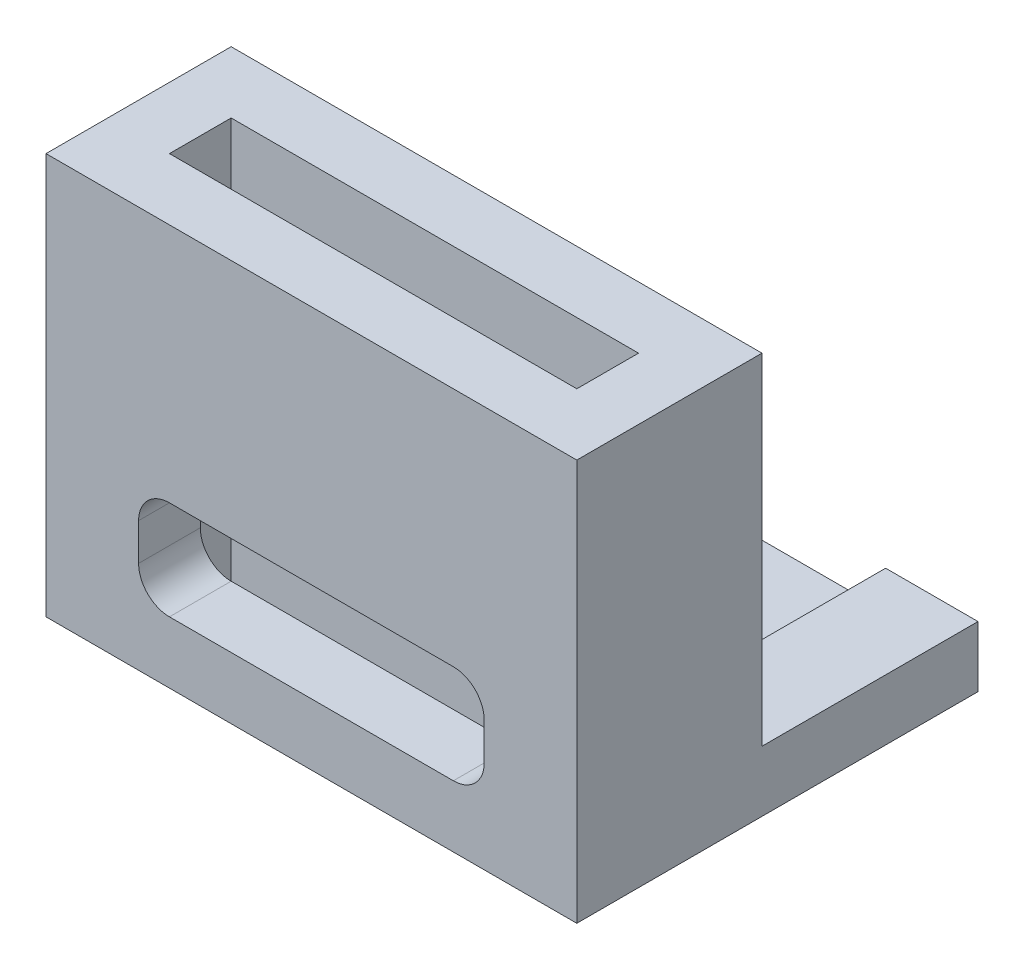
SolidWorks part; units mm, degrees
ref_plane "Front Plane" through (0, 0, 0) normal (0, 0, 1) x (1, 0, 0)
ref_plane "Top Plane" through (0, 0, 0) normal (0, 1, 0) x (1, 0, 0)
ref_plane "Right Plane" through (0, 0, 0) normal (1, 0, 0) x (0, 0, -1)
sketch "Sketch1" plane through (0, 0, 0) normal (0, 1, 0) x (1, 0, 0)
  line L0 (0, 0) -> (13.2, 0)
  line L1 (0, 0) -> (0, 2)
  line L2 (0, 2) -> (13.2, 2)
  line L3 (13.2, 2) -> (13.2, 0)
  line L4 (15.2, 4) -> (15.2, -2)
  line L5 (-2, -2) -> (15.2, -2)
  line L6 (-2, -2) -> (-2, 4)
  line L7 (-2, 4) -> (15.2, 4)
  dimension "D1" = 2
extrude "Boss-Extrude1" add sketch "Sketch1" along normal blind 13
sketch "Sketch2" plane through (0, 0, 2) normal (0, 0, 1) x (1, 0, 0)
  line L4 (2, 5.2) -> (11.2, 5.2)
  line L5 (1, 4.2) -> (1, 3)
  line L6 (2, 2) -> (11.2, 2)
  line L7 (12.2, 3) -> (12.2, 4.2)
  arc A1 (11.2, 2) -> (12.2, 3) centre (11.2, 3) ccw
  arc A2 (12.2, 4.2) -> (11.2, 5.2) centre (11.2, 4.2) ccw
  arc A3 (2, 5.2) -> (1, 4.2) centre (2, 4.2) ccw
  arc A4 (1, 3) -> (2, 2) centre (2, 3) ccw
  dimension "D1" = 1
extrude "Cut-Extrude1" cut sketch "Sketch2" against normal blind 13 contours L4 A2 L7 A1 L6 A4 L5 A3
sketch "Sketch4" plane through (0, 0, -4) normal (0, 0, -1) x (-1, 0, 0)
  line L0 (2, 13) -> (2, 0) construction
  line L1 (-15.2, 0) -> (2, 0)
  line L2 (-15.2, 0) -> (-15.2, 1.969)
  line L3 (-15.2, 1.969) -> (2, 1.969)
  line L4 (2, 0) -> (2, 1.969)
extrude "Boss-Extrude2" add sketch "Sketch4" along normal blind 7
sketch "Sketch5" plane through (0, 1.969, 0) normal (0, 1, 0) x (1, 0, 0)
  circle A0 centre (6.6, 7.5) radius 1.6
extrude "Cut-Extrude2" cut sketch "Sketch5" against normal blind 4
sketch "Sketch6" plane through (0, 0, -11) normal (0, 0, -1) x (-1, 0, 0)
  line L0 (-1, 4.2) -> (-1, 3) construction
  line L1 (-12.2065, 0.7524) -> (-1, 0.7524)
  line L2 (-12.2065, 0.7524) -> (-12.2065, 3.2384)
  line L3 (-12.2065, 3.2384) -> (-1, 3.2384)
  line L4 (-1, 0.7524) -> (-1, 3.2384)
extrude "Cut-Extrude3" cut sketch "Sketch6" against normal up to surface (7 mm away) up to face at (6.6, 3.6, -4)
